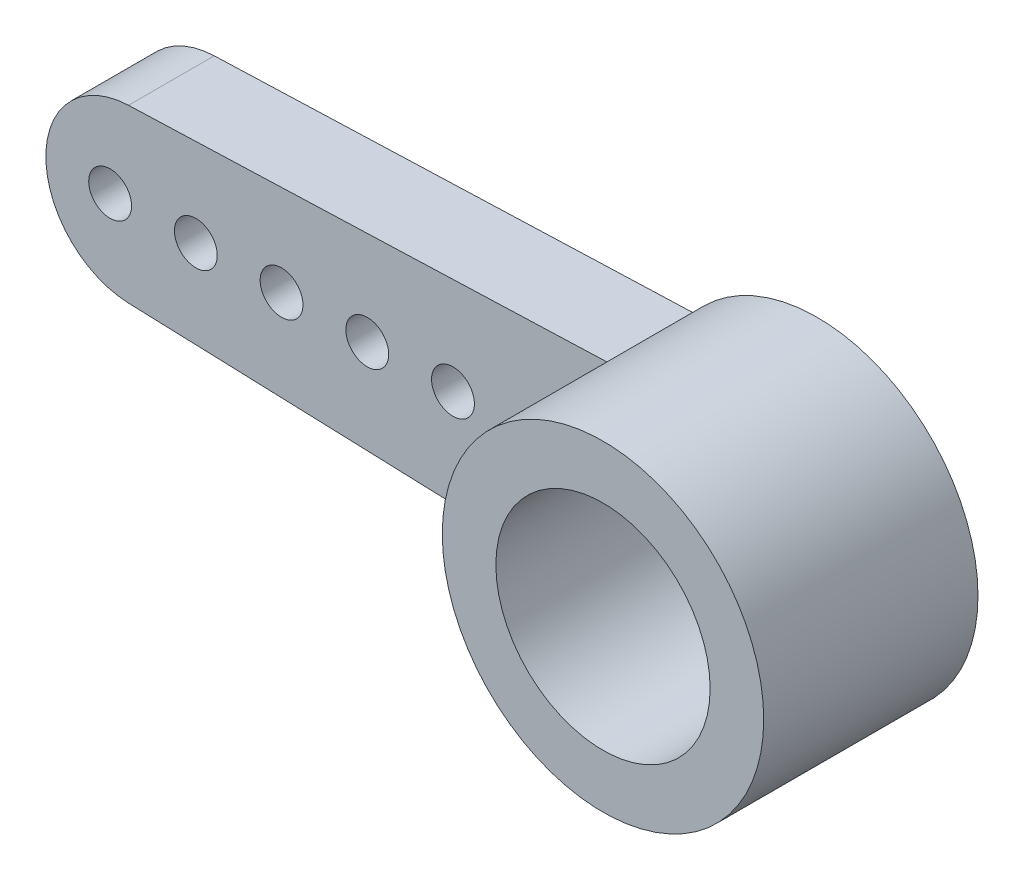
SolidWorks part; units mm, degrees
ref_plane "Спереди" through (0, 0, 0) normal (0, 0, 1) x (1, 0, 0)
ref_plane "Сверху" through (0, 0, 0) normal (0, 1, 0) x (1, 0, 0)
ref_plane "Справа" through (0, 0, 0) normal (1, 0, 0) x (0, 0, -1)
sketch "Эскиз1" plane through (0, 0, 0) normal (0, 0, 1) x (1, 0, 0)
  line L0 (0, 0) -> (-14, 0)
  line L1 (-14.0708, 1.9987) -> (0, 2.4974)
  line L2 (-14.0708, -1.9987) -> (0, -2.4974)
  line L4 (14.0708, -1.9987) -> (0, -2.4974)
  line L5 (14.0708, 1.9987) -> (0, 2.4974)
  circle A0 centre (0, 0) radius 3.75
  circle A1 centre (0, 0) radius 2.5
  arc A2 (-13.967, -1.9997) -> (-14.0708, 1.9987) centre (-14, 0) cw
  arc A3 (13.967, -1.9997) -> (14.0708, 1.9987) centre (14, 0) ccw
  dimension "D1" = 7.5
  dimension "D2" = 5
  dimension "D4" = 2
  dimension "D3" = 14
extrude "Бобышка-Вытянуть3" add sketch "Эскиз1" along normal blind 2
sketch "Эскиз2" plane through (0, 0, 2) normal (0, 0, 1) x (1, 0, 0)
  circle A0 centre (0, 0) radius 3.75
  circle A1 centre (0, 0) radius 2.5
  dimension "D1" = 5
extrude "Бобышка-Вытянуть5" add sketch "Эскиз2" along normal blind 3 separate body
sketch "Эскиз3" plane through (0, 0, 2) normal (0, 0, -1) x (-1, 0, 0)
  circle A0 centre (0, 0) radius 3.75
  circle A1 centre (0, 0) radius 2.5
extrude "Бобышка-Вытянуть6" add sketch "Эскиз3" along normal blind 2
sketch "Эскиз4" plane through (0, 0, 0) normal (0, 0, -1) x (-1, 0, 0)
  line L0 (-16, 0) -> (-14.5, 0)
  line L1 (-14.5, 0) -> (-12.5, 0)
  line L2 (-12.5, 0) -> (-10.5, 0)
  line L3 (-10.5, 0) -> (-8.5, 0)
  line L4 (-8.5, 0) -> (-6.5, 0)
  line L5 (-6.5, 0) -> (-4.5, 0)
  arc A0 (-14.0708, 1.9987) -> (-14.0708, -1.9987) centre (-14, 0) ccw construction
  circle A1 centre (-14.5, 0) radius 0.5
  circle A2 centre (-12.5, 0) radius 0.5
  circle A3 centre (-10.5, 0) radius 0.5
  circle A4 centre (-8.5, 0) radius 0.5
  circle A5 centre (-6.5, 0) radius 0.5
  circle A6 centre (-4.5, 0) radius 0.5
  circle A7 centre (4.5, 0) radius 0.5
  circle A8 centre (6.5, 0) radius 0.5
  circle A9 centre (8.5, 0) radius 0.5
  circle A10 centre (10.5, 0) radius 0.5
  circle A11 centre (12.5, 0) radius 0.5
  circle A12 centre (14.5, 0) radius 0.5
  dimension "D2" = 1
  dimension "D8" = 1
  dimension "D9" = 1
  dimension "D10" = 1
  dimension "D11" = 1
  dimension "D12" = 1
  dimension "D1" = 1.5
  dimension "D3" = 2
  dimension "D4" = 2
  dimension "D5" = 2
  dimension "D6" = 2
  dimension "D7" = 2
extrude "Вырез-Вытянуть1" cut sketch "Эскиз4" against normal blind 2
sketch "Эскиз5" plane through (0, 0, 0) normal (0, 0, -1) x (-1, 0, 0)
  circle A0 centre (0, 0) radius 2.5
extrude "Бобышка-Вытянуть7" add sketch "Эскиз5" against normal blind 1
sketch "Эскиз6" plane through (0, 0, 0) normal (0, 0, -1) x (-1, 0, 0)
  circle A0 centre (0, 0) radius 2.5
  dimension "D1" = 5
extrude "Вырез-Вытянуть2" cut sketch "Эскиз6" against normal blind 0.5
sketch "Эскиз7" plane through (0, 0, 0.5) normal (0, 0, -1) x (-1, 0, 0)
  circle A0 centre (0, 0) radius 1.25
  dimension "D1" = 2.5
extrude "Вырез-Вытянуть3" cut sketch "Эскиз7" against normal blind 5
sketch "Эскиз8" plane through (0, 0, 0.5) normal (0, 0, -1) x (-1, 0, 0)
  line L0 (-2.8252, -0.1999) -> (-2.8894, -0.2509)
sketch "Sketch1" plane through (0, 0, 5) normal (0, 0, 1) x (1, 0, 0)
  line L2 (2.8855, -2.3951) -> (14.0708, -1.9987)
  line L3 (14.0708, 1.9987) -> (2.8855, 2.3951)
  line L4 (2.8855, -2.3951) -> (14.0708, -1.9987)
  line L5 (14.0708, 1.9987) -> (2.8855, 2.3951)
  arc A0 (2.8855, -2.3951) -> (2.8855, 2.3951) centre (0, 0) ccw
  arc A3 (2.8855, -2.3951) -> (2.8855, 2.3951) centre (0, 0) ccw
  arc A4 (14.0708, -1.9987) -> (14.0708, 1.9987) centre (14, 0) ccw
  arc A5 (2.8855, -2.3951) -> (2.8855, 2.3951) centre (0, 0) ccw
  arc A6 (14.0708, -1.9987) -> (14.0708, 1.9987) centre (14, 0) ccw
  circle M1 centre (0, 0) radius 3.75
  dimension "D1" = 0
extrude "Cut-Extrude1" cut sketch "Sketch1" against normal through all contours L4 A6 L5 M1
